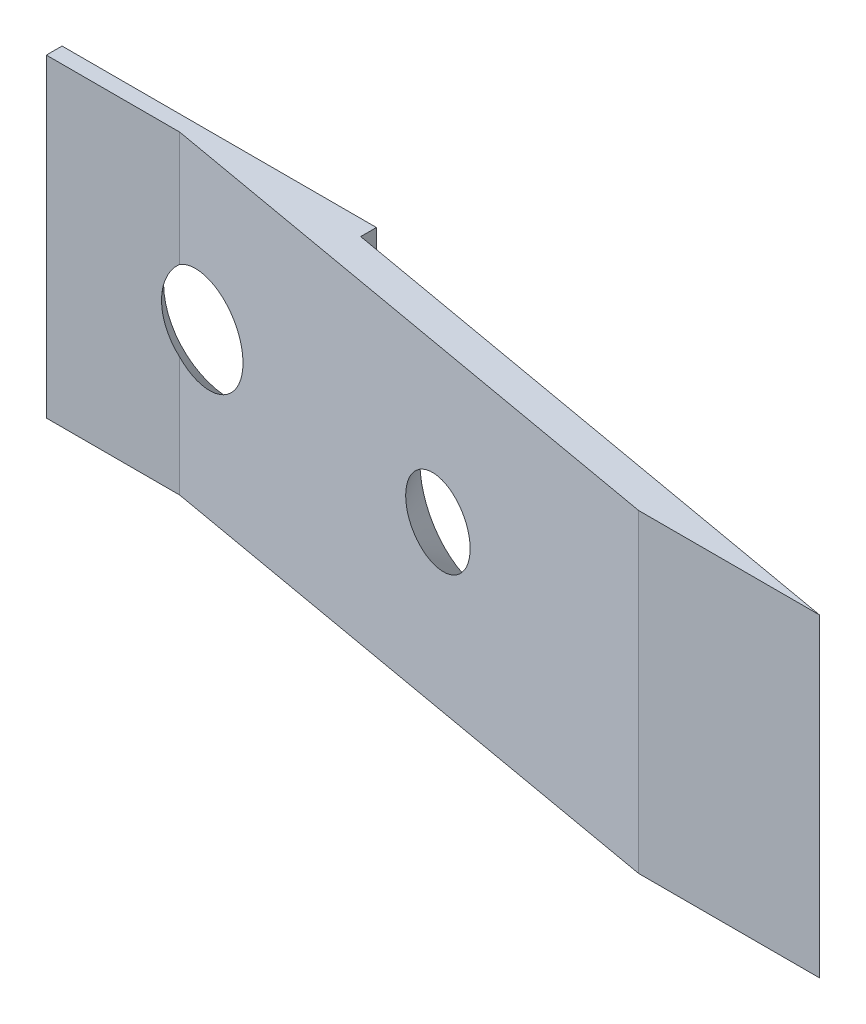
SolidWorks part; units mm, degrees
ref_plane "Front Plane" through (0, 0, 0) normal (0, 0, 1) x (1, 0, 0)
ref_plane "Top Plane" through (0, 0, 0) normal (0, 1, 0) x (1, 0, 0)
ref_plane "Right Plane" through (0, 0, 0) normal (1, 0, 0) x (0, 0, -1)
sketch "Sketch2" plane through (0, 0, 0) normal (0, 0, 1) x (1, 0, 0)
  line L0 (5, 0) -> (5, -10) construction
  line L1 (0, 0) -> (10, 0)
  line L2 (0, 0) -> (0, -10)
  line L3 (0, -10) -> (10, -10)
  line L4 (10, 0) -> (10, -10)
  line L5 (5, -10) -> (0, -5) construction
  line L6 (0, -5) -> (10.1099, -5) construction
  dimension "D1" = 10
  dimension "D2" = 10
extrude "Boss-Extrude1" add sketch "Sketch2" along normal blind 0.5
sketch "Sketch3" plane through (0, -10, 0) normal (0, -1, 0) x (1, 0, 0)
  line L0 (4.2412, 0.5) -> (21.9678, 3.6257)
  line L1 (0, 0.5) -> (10, 0.5) construction
  line L2 (21.9678, 3.6257) -> (27.7265, 3.6257)
  line L3 (27.7265, 3.6257) -> (10, 0.5)
  line L4 (10, 0.5) -> (4.2412, 0.5)
  dimension "D1" = 170
  dimension "D2" = 18
  dimension "D3" = 1
extrude "Boss-Extrude2" add sketch "Sketch3" against normal blind 10
sketch "Sketch6" plane through (0, 0, 0) normal (0, 0, -1) x (-1, 0, 0)
  point P0 (-5.3625, -4.9213)
hole_wizard "CSK for #1 Flat Head Socket Cap Screw1" positions "Sketch6" profile "Sketch7" countersink size "#1" standard "ANSI Inch" end condition through all
sketch "Sketch7" plane through (5.3625, -4.9213, 0) normal (1, 0, 0) x (0, 1, 0)
  line L0 (0, 0) -> (0, 3.6257)
  line L1 (0, 3.6257) -> (1.0287, 3.6257)
  line L2 (1.0287, 3.6257) -> (1.0287, 1.271)
  line L3 (1.0287, 1.271) -> (2.1336, 0)
  line L5 (2.1336, 0) -> (0, 0)
  line L6 (-1.0287, 1.271) -> (-2.1336, 0) construction
  line L11 (0, -6.35) -> (0, 107.95) construction
  dimension "Thru Hole Dia." = 2.0574
  dimension "Thru Hole Depth" = 3.6257
  dimension "Near C'Sink Dia." = 4.2672
  dimension "Near C'Sink Angle" = 82
sketch "Sketch8" plane through (0.216, 0, -1.2252) normal (0.1736, 0, -0.9848) x (-0.9848, 0, -0.1736)
  point P0 (-14.3915, -4.8794)
hole_wizard "CSK for #1 Flat Head Socket Cap Screw2" positions "Sketch8" profile "Sketch9" countersink size "#1" standard "ANSI Inch" end condition through all
sketch "Sketch9" plane through (14.3889, -4.8794, 1.2739) normal (0, 1, 0) x (-0.9848, 0, -0.1736)
  line L0 (0, 0) -> (0, 4.8147)
  line L1 (0, 4.8147) -> (1.0287, 4.8147)
  line L2 (1.0287, 4.8147) -> (1.0287, 1.271)
  line L3 (1.0287, 1.271) -> (2.1336, 0)
  line L5 (2.1336, 0) -> (0, 0)
  line L6 (-1.0287, 1.271) -> (-2.1336, 0) construction
  line L11 (0, -6.35) -> (0, 107.95) construction
  dimension "Thru Hole Dia." = 2.0574
  dimension "Thru Hole Depth" = 4.8147
  dimension "Near C'Sink Dia." = 4.2672
  dimension "Near C'Sink Angle" = 82
